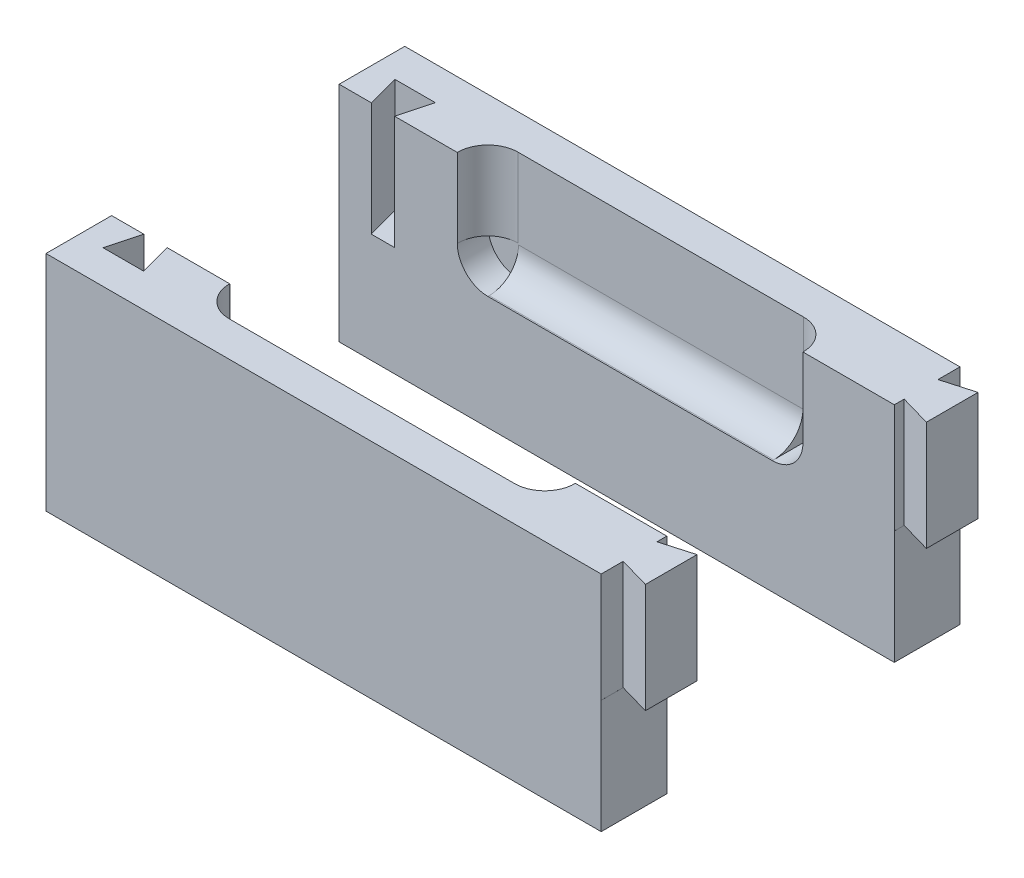
SolidWorks part; units mm, degrees
ref_plane "Front Plane" through (0, 0, 0) normal (0, 0, 1) x (1, 0, 0)
ref_plane "Top Plane" through (0, 0, 0) normal (0, 1, 0) x (1, 0, 0)
ref_plane "Right Plane" through (0, 0, 0) normal (1, 0, 0) x (0, 0, -1)
sketch "Sketch1" plane through (0, 0, 0) normal (0, 0, 1) x (1, 0, 0)
  line L1 (-60.9366, 28.6127) -> (73.0634, 28.6127)
  line L2 (-60.9366, 28.6127) -> (-60.9366, -22.3873)
  line L3 (-60.9366, -22.3873) -> (73.0634, -22.3873)
  line L4 (73.0634, 28.6127) -> (73.0634, -22.3873)
  dimension "D1" = 51
  dimension "D2" = 134
extrude "Boss-Extrude1" add sketch "Sketch1" along normal blind 15
ref_plane "Plane4" through (38.0634, 0, 0) normal (1, 0, 0) x (0, 0, -1)
sketch "Sketch8" plane through (38.0634, 0, 0) normal (1, 0, 0) x (0, 0, -1)
  line L0 (-15, 28.6127) -> (0, 28.6127) construction
  line L1 (-7, 28.6127) -> (0, 28.6127)
  line L2 (-7, 28.6127) -> (-7, 10.3127)
  line L3 (-0.3, 3.6127) -> (0, 3.6127)
  line L4 (0, 28.6127) -> (0, 3.6127)
  arc A0 (-0.3, 3.6127) -> (-7, 10.3127) centre (-0.3, 10.3127) cw
  dimension "D2" = 6.7
  dimension "D1" = 25
extrude "Cut-Extrude6" cut sketch "Sketch8" against normal blind 65
sketch "Sketch3" plane through (0, 28.6127, 0) normal (0, 1, 0) x (1, 0, 0)
  line L0 (-60.9366, 0) -> (-53.5866, 0)
  line L2 (-26.9366, 0) -> (-60.9366, 0) construction
  line L3 (-53.5866, 0) -> (-55.5536, -7.341)
  line L4 (-55.5536, -7.341) -> (-46.3196, -7.341)
  line L5 (-46.3196, -7.341) -> (-48.2866, 0)
  dimension "D1" = 7.35
  dimension "D2" = 105
  dimension "D3" = 105
  dimension "D4" = 75
  dimension "D5" = 75
  dimension "D6" = 7.6
  dimension "D7" = 7.6
  dimension "D8" = 5.3
  dimension "D9" = 9.234
extrude "Cut-Extrude2" cut sketch "Sketch3" against normal blind 26 and the other way through all
sketch "Sketch5" plane through (0, 28.6127, 0) normal (0, 1, 0) x (1, 0, 0)
  line L3 (65.95, 0) -> (73.0634, 0)
  line L4 (73.0634, 0) -> (38.0634, 0) construction
  line L5 (73.0634, 0) -> (73.0634, -0.2103)
  line L6 (73.0634, -15) -> (73.0634, 0) construction
  line L7 (73.0634, -0.2103) -> (65.95, -2.25)
  line L8 (65.95, -2.25) -> (65.95, 0)
  line L9 (65.95, -15) -> (65.95, -9.9706)
  line L10 (73.0634, -15) -> (-60.9366, -15) construction
  line L11 (65.95, -9.9706) -> (73.0634, -12.0103)
  line L12 (73.0634, -12.0103) -> (73.0634, -15)
  line L13 (73.0634, -15) -> (65.95, -15)
  dimension "D1" = 7.4
  dimension "D2" = 7.4
  dimension "D3" = 106
  dimension "D4" = 7.1133
  dimension "D5" = 11.8
  dimension "D6" = 2.25
extrude "Cut-Extrude4" cut sketch "Sketch5" against normal blind 25
sketch "Sketch7" plane through (0, -22.3873, 0) normal (0, -1, 0) x (1, 0, 0)
  line L0 (-60.9366, 0) -> (73.0634, 0) construction
  line L1 (65.9534, 0) -> (73.0634, 0)
  line L2 (65.9534, 0) -> (65.9534, 15)
  line L3 (65.9534, 15) -> (73.0634, 15)
  line L4 (73.0634, 0) -> (73.0634, 15)
  dimension "D1" = 7.11
extrude "Cut-Extrude5" cut sketch "Sketch7" against normal blind 26
ref_plane "Plane3" through (0, 0, -26) normal (0, 0, -1) x (-1, 0, 0)
sketch "Sketch9" plane through (0, 28.6127, 0) normal (0, 1, 0) x (1, 0, 0)
  line L0 (-26.9366, 0) -> (-48.2866, 0) construction
  line L1 (-26.9366, -7) -> (-27.0366, -7)
  line L2 (-26.9366, -7) -> (-26.9366, 0)
  line L3 (-26.9366, 0) -> (-33.9366, 0)
  line L4 (-33.9366, -0.1) -> (-33.9366, 0)
  line L5 (38.0634, -6.49) -> (38.0634, 6.49) construction
  line L6 (38.0634, -7) -> (38.1634, -7)
  line L7 (38.0634, -7) -> (38.0634, 0)
  line L8 (38.0634, 0) -> (45.0634, 0)
  line L9 (45.0634, -0.1) -> (45.0634, 0)
  line L10 (65.95, 0) -> (38.0634, 0) construction
  arc A0 (-27.0366, -7) -> (-33.9366, -0.1) centre (-27.0366, -0.1) cw
  arc A1 (45.0634, -0.1) -> (38.1634, -7) centre (38.1634, -0.1) cw
  dimension "D4" = 6.9
  dimension "D2" = 6.9
  dimension "D1" = 7
  dimension "D3" = 7
extrude "Cut-Extrude7" cut sketch "Sketch9" against normal blind 18
sketch "Sketch12" plane through (0, 0, 0) normal (0, 0, -1) x (-1, 0, 0)
  line L0 (-45.0634, 10.6127) -> (-38.0634, 10.6127) construction
  line L1 (-38.1634, 10.6127) -> (-45.0634, 10.6127) construction
  line L2 (26.9366, 3.6127) -> (-38.0634, 3.6127) construction
  line L3 (-45.0634, 10.6127) -> (-38.0634, 10.6127)
  line L4 (-38.0634, 10.6127) -> (-38.0634, 3.6127)
  line L5 (26.9366, 3.6127) -> (26.9366, 10.6127)
  line L6 (26.9366, 10.6127) -> (33.9366, 10.6127)
  arc A0 (-45.0634, 10.6127) -> (-38.0634, 3.6127) centre (-38.0634, 10.6127) ccw
  arc A1 (33.9366, 10.6127) -> (26.9366, 3.6127) centre (26.9366, 10.6127) cw
  line M3 (33.9366, 10.6127) -> (26.9366, 10.6127)
  line M4 (26.9366, 10.6127) -> (26.9366, 3.6127)
  line M6 (-38.0634, 3.6127) -> (-38.0634, 10.6127)
  line M7 (-38.0634, 10.6127) -> (-45.0634, 10.6127)
extrude "Cut-Extrude8" cut sketch "Sketch12" against normal blind 7 contours A0 M7 M6 | A1 M3 M4
mirror "Mirror2" about plane through (0, 0, -26) normal (0, 0, -1) of bodies 111 107
